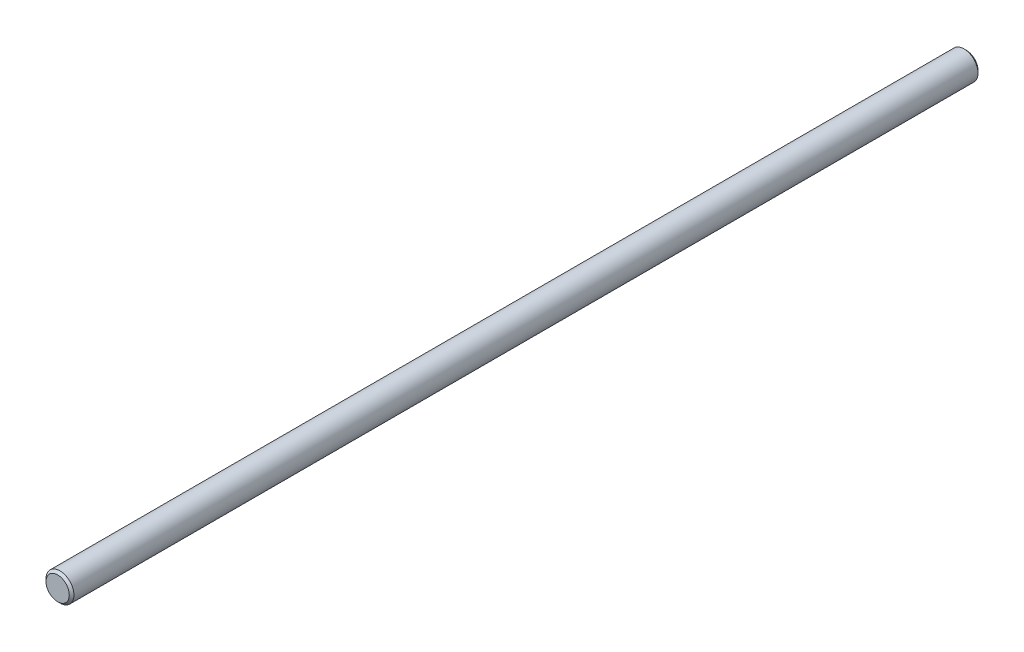
SolidWorks part; units mm, degrees
ref_plane "Piano frontale" through (0, 0, 0) normal (0, 0, 1) x (1, 0, 0)
ref_plane "Piano superiore" through (0, 0, 0) normal (0, 1, 0) x (1, 0, 0)
ref_plane "Piano destro" through (0, 0, 0) normal (1, 0, 0) x (0, 0, -1)
sketch "Schizzo1" plane through (0, 0, 0) normal (0, 0, 1) x (1, 0, 0)
  circle A0 centre (0, 0) radius 6
  dimension "D1" = 12
extrude "Estrusione-Estrusione1" add sketch "Schizzo1" along normal blind 390
chamfer "Smusso1" distance 1 angle 45 2 edges at (6, 0, 390) (6, 0, 0)
